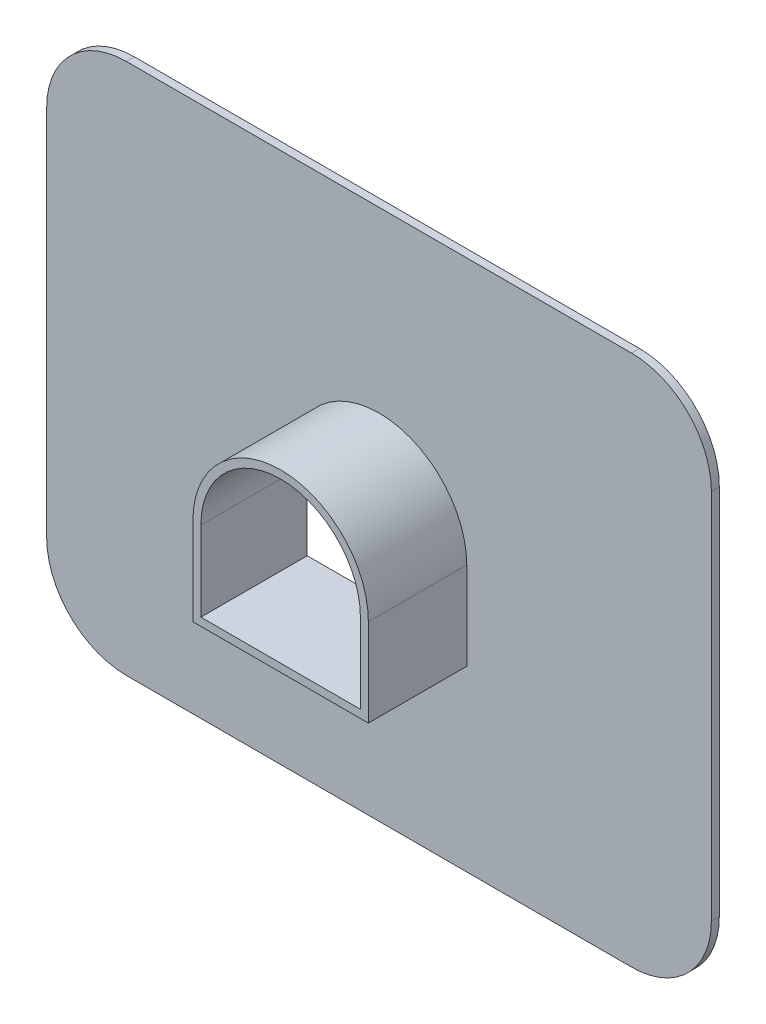
SolidWorks part; units mm, degrees
ref_plane "Plan de face" through (0, 0, 0) normal (0, 0, 1) x (1, 0, 0)
ref_plane "Plan de dessus" through (0, 0, 0) normal (0, 1, 0) x (1, 0, 0)
ref_plane "Plan de droite" through (0, 0, 0) normal (1, 0, 0) x (0, 0, -1)
sketch "Esquisse1" plane through (0, 0, 0) normal (0, 0, 1) x (1, 0, 0)
  line L0 (-3, -3) -> (3, -3)
  line L1 (-9.5, 10) -> (9.5, 10)
  line L2 (-12.5, 7) -> (-12.5, -7)
  line L3 (-9.5, -10) -> (9.5, -10)
  line L4 (12.5, 7) -> (12.5, -7)
  line L5 (3, -3) -> (3, 0)
  line L6 (-3, -3) -> (-3, 0)
  arc A0 (-3, 0) -> (3, 0) centre (0, 0) cw
  arc A1 (9.5, 10) -> (12.5, 7) centre (9.5, 7) cw
  arc A2 (-12.5, 7) -> (-9.5, 10) centre (-9.5, 7) cw
  arc A3 (-9.5, -10) -> (-12.5, -7) centre (-9.5, -7) cw
  arc A4 (12.5, -7) -> (9.5, -10) centre (9.5, -7) cw
  point P12 (12.5, 10)
  point P15 (-12.5, 10)
  point P20 (12.5, -10)
  dimension "D6" = 3
  dimension "D7" = 3
  dimension "D1" = 25
  dimension "D2" = 20
  dimension "D3" = 10
  dimension "D4" = 12.5
  dimension "D5" = 6
extrude "Extrusion1" add sketch "Esquisse1" along normal blind 0.3
sketch "Esquisse2" plane through (0, 0, 0.3) normal (0, 0, 1) x (1, 0, 0)
  line L0 (-3, -3) -> (3, -3)
  line L1 (-3, -3) -> (3, -3) construction
  line L2 (3, -3) -> (3, 0)
  line L3 (-3, 0) -> (-3, -3) construction
  line L4 (-3, 0) -> (-3, -3)
  line L5 (-3.3, -3.3) -> (3.3, -3.3)
  line L6 (3.3, -3.3) -> (3.3, 0)
  line L7 (-3.3, 0) -> (-3.3, -3.3)
  arc A0 (3, 0) -> (-3, 0) centre (0, 0) ccw
  arc A1 (3, 0) -> (-3, 0) centre (0, 0) ccw construction
  arc A2 (3.3, 0) -> (-3.3, 0) centre (0, 0) ccw
  dimension "D1" = 0.3
extrude "Extrusion2" add sketch "Esquisse2" along normal blind 3.7
